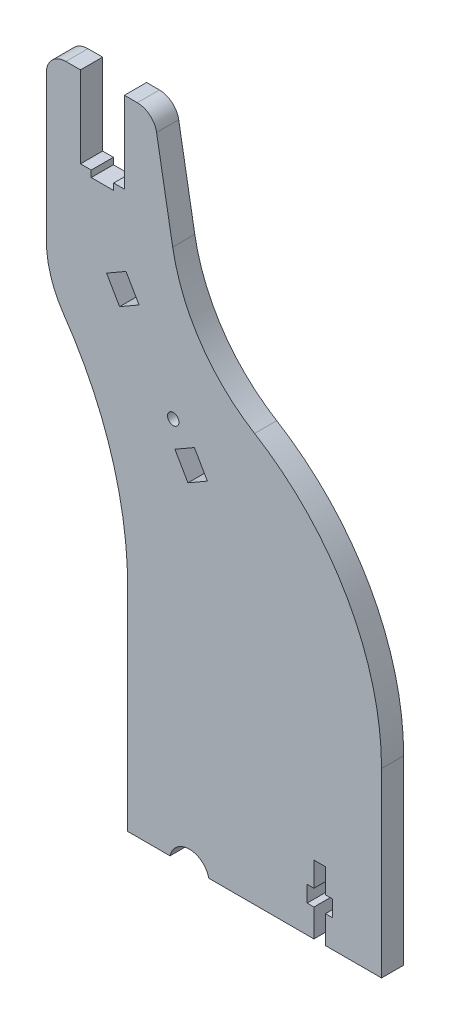
SolidWorks part; units mm, degrees
ref_plane "Front Plane" through (0, 0, 0) normal (0, 0, 1) x (1, 0, 0)
ref_plane "Top Plane" through (0, 0, 0) normal (0, 1, 0) x (1, 0, 0)
ref_plane "Right Plane" through (0, 0, 0) normal (1, 0, 0) x (0, 0, -1)
sketch "Sketch1" plane through (0, 0, 0) normal (0, 0, 1) x (1, 0, 0)
  line L0 (-97, 195.4) -> (-92.5, 195.4)
  line L1 (-92.5, 170.4) -> (-92.5, 195.4)
  line L2 (-89.2, 168.4) -> (-89.2, 170.4)
  line L3 (-82.3, 168.4) -> (-89.2, 168.4)
  line L4 (-82.3, 170.4) -> (-82.3, 168.4)
  line L5 (-79, 170.4) -> (-82.3, 170.4)
  line L6 (-79, 195.4) -> (-79, 170.4)
  line L7 (-79, 195.4) -> (-75.0346, 195.4)
  line L8 (-64.1812, 162.4) -> (-69.1258, 190.4419)
  line L9 (-89.2, 170.4) -> (-92.5, 170.4)
  line L10 (0, 0) -> (0, 55.7267)
  line L11 (-78, 0) -> (-78, 64.6706)
  line L12 (-103, 189.4) -> (-103, 144.8603)
  line L13 (0, 0) -> (-78, 0)
  arc A0 (-97, 195.4) -> (-103, 189.4) centre (-97, 189.4) ccw
  arc A1 (-69.1258, 190.4419) -> (-75.0346, 195.4) centre (-75.0346, 189.4) ccw
  arc A2 (-64.1812, 162.4) -> (-39, 125.4) centre (-10.4994, 171.8655) ccw
  arc A3 (0, 55.7267) -> (-39, 125.4) centre (-81.7355, 55.7267) ccw
  arc A4 (-78, 64.6706) -> (-97.6524, 127.7647) centre (-188.2515, 64.9374) ccw
  arc A5 (-103, 144.8603) -> (-97.6524, 127.7647) centre (-73, 144.8603) ccw
  dimension "D2" = 6
  dimension "D3" = 54.5099
  dimension "D4" = 81.7355
  dimension "D5" = 110.2518
  dimension "D6" = 30
  dimension "D1" = 78
  dimension "D7" = 10.4994
  dimension "D8" = 64.1812
  dimension "D9" = 69.1258
  dimension "D10" = 73
  dimension "D11" = 79
  dimension "D12" = 82.3
  dimension "D13" = 89.2
  dimension "D14" = 97.6524
  dimension "D15" = 55.7267
  dimension "D16" = 64.6706
  dimension "D17" = 168.4
  dimension "D18" = 170.4
extrude "Boss-Extrude1" add sketch "Sketch1" along normal blind 6.8
sketch "Sketch2" plane through (0, 0, 6.8) normal (0, 0, 1) x (1, 0, 0)
  line L0 (-78, 0) -> (0, 0) construction
  line L1 (-17.225, 0) -> (-20.775, 0)
  line L2 (-17.225, 0) -> (-17.225, 21)
  line L3 (-17.225, 21) -> (-20.775, 21)
  line L4 (-20.775, 0) -> (-20.775, 21)
  line L5 (-17.225, 0) -> (-20.775, 21) construction
  line L6 (-17.225, 21) -> (-20.775, 0) construction
  line L7 (0, 0) -> (0, 55.7267) construction
  line L9 (-22.86, 8.5) -> (-15.14, 8.5)
  line L10 (-22.86, 8.5) -> (-22.86, 13.5)
  line L11 (-22.86, 13.5) -> (-15.14, 13.5)
  line L12 (-15.14, 8.5) -> (-15.14, 13.5)
  line L13 (-22.86, 8.5) -> (-15.14, 13.5) construction
  line L14 (-22.86, 13.5) -> (-15.14, 8.5) construction
  point P0 (-19, 10.5)
  point P9 (-19, 11)
  line M12 (-78, 0) -> (0, 0)
  dimension "D1" = 3.55
  dimension "D2" = 19
  dimension "D3" = 21
  dimension "D4" = 8.5
  dimension "D5" = 7.72
  dimension "D6" = 5
extrude "Cut-Extrude1" cut sketch "Sketch2" against normal blind 6.8 contours L4 L11 L2 L3 | L11 L10 L9 L4 | L9 L12 L11 L2 | L9 L4 L2 M12 | L11 L4 L9 L2
sketch "Sketch3" plane through (0, 0, 6.8) normal (0, 0, 1) x (1, 0, 0)
  line L0 (-78, 0) -> (-20.775, 0) construction
  line L1 (0, 0) -> (0, 55.7267) construction
  circle A0 centre (-59.04, -1.3381) radius 6.1
  dimension "D2" = 12.2
  dimension "D1" = 1.3381
  dimension "D3" = 59.04
extrude "Cut-Extrude2" cut sketch "Sketch3" against normal blind 6.8
sketch "Sketch4" plane through (0, 0, 0) normal (0, 0, -1) x (-1, 0, 0)
  line L2 (103, 189.4) -> (103, 144.8603) construction
  line L3 (78, 0) -> (64.9914, 0) construction
  line L10 (84.488, 145.3263) -> (78.5124, 148.7763)
  line L11 (78.5124, 148.7763) -> (74.5124, 141.8481)
  line L12 (74.5124, 141.8481) -> (80.488, 138.3981)
  line L13 (80.488, 138.3981) -> (84.488, 145.3263)
  line L18 (63.488, 108.9532) -> (57.5124, 112.4032)
  line L19 (57.5124, 112.4032) -> (53.5124, 105.475)
  line L20 (53.5124, 105.475) -> (59.488, 102.025)
  line L21 (59.488, 102.025) -> (63.488, 108.9532)
  circle A0 centre (64.0002, 116.7404) radius 1.75
extrude "Cut-Extrude3" cut sketch "Sketch4" against normal blind 6.8
